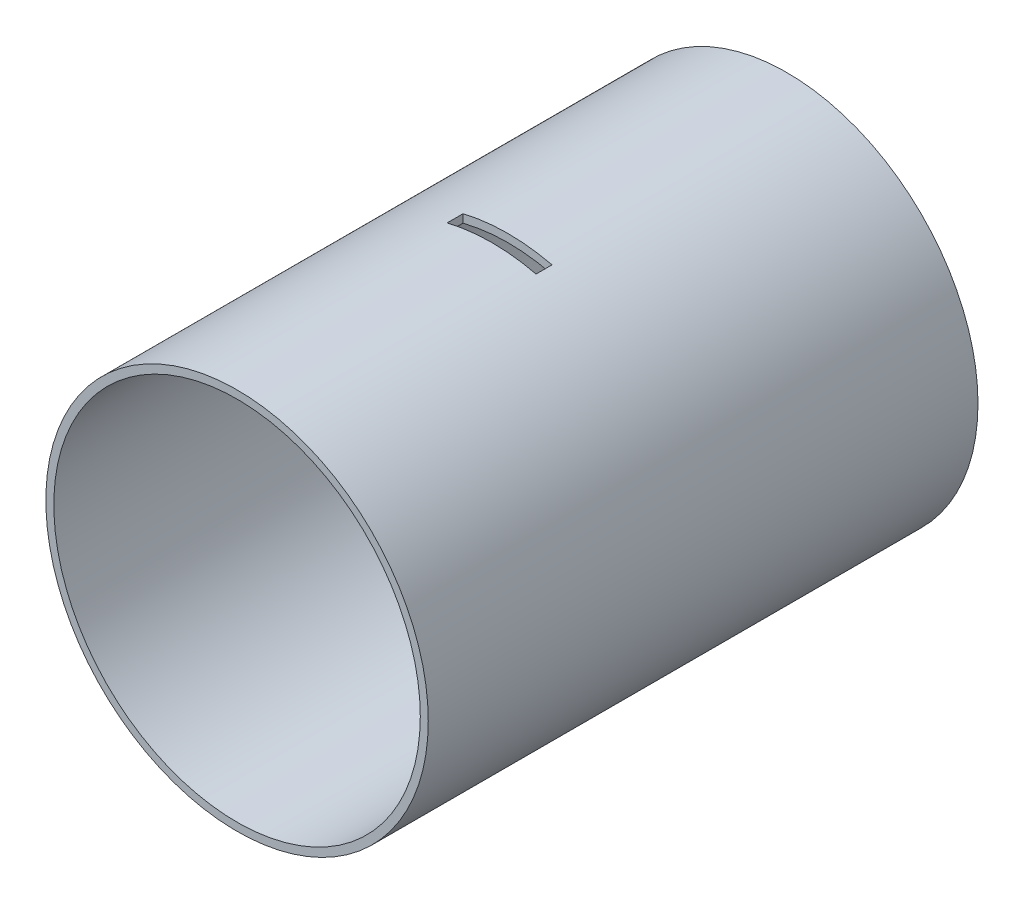
SolidWorks part; units mm, degrees
material "Balsa"
ref_plane "Front Plane" through (0, 0, 0) normal (0, 0, 1) x (1, 0, 0)
ref_plane "Top Plane" through (0, 0, 0) normal (0, 1, 0) x (1, 0, 0)
ref_plane "Right Plane" through (0, 0, 0) normal (1, 0, 0) x (0, 0, -1)
sketch "Sketch1" plane through (0, 0, 0) normal (0, 0, 1) x (1, 0, 0)
  circle A0 centre (0, 0) radius 152.4
  circle A1 centre (0, 0) radius 146.05
extrude "Boss-Extrude1" add sketch "Sketch1" along normal blind 438.15
sketch "Sketch2" plane through (0, 0, 0) normal (0, 1, 0) x (1, 0, 0)
  line L0 (0, 0) -> (0, -222.25) construction
  line L2 (-35.7791, -222.25) -> (-35.7791, -234.95)
  line L5 (-35.7791, -222.25) -> (35.1399, -222.25)
  line L6 (-35.7791, -234.95) -> (35.1399, -234.95)
  line L7 (35.1399, -234.95) -> (35.1399, -222.25)
extrude "Cut-Extrude1" cut sketch "Sketch2" against normal mid plane 800.1
sketch "Sketch3" plane through (0, 0, 0) normal (1, 0, 0) x (0, 0, -1)
  line L3 (-230.2118, 12.7116) -> (-230.2118, -12.7116) construction
  line L5 (-222.25, -12.7116) -> (-234.95, -12.7116)
  line L6 (-234.95, -12.7116) -> (-234.95, 12.7116)
  line L7 (-234.95, 12.7116) -> (-222.25, 12.7116)
  line L8 (-222.25, 12.7116) -> (-222.25, -12.7116)
  line L9 (-222.25, 0) -> (0, 0) construction
extrude "Cut-Extrude2" cut sketch "Sketch3" against normal blind 508
